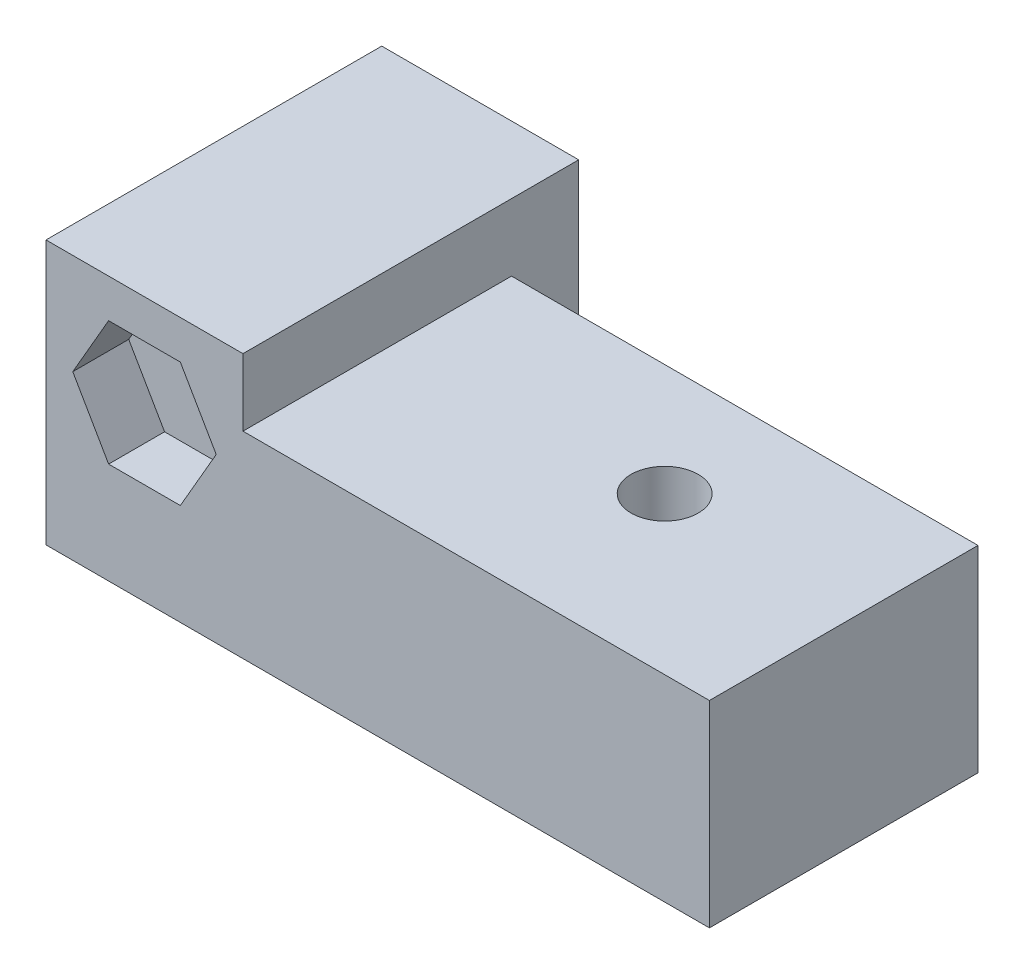
SolidWorks part; units mm, degrees
material "ABS"
ref_plane "前视基准面" through (0, 0, 0) normal (0, 0, 1) x (1, 0, 0)
ref_plane "上视基准面" through (0, 0, 0) normal (0, 1, 0) x (1, 0, 0)
ref_plane "右视基准面" through (0, 0, 0) normal (1, 0, 0) x (0, 0, -1)
sketch "草图1" plane through (0, 0, 0) normal (0, 0, 1) x (1, 0, 0)
  line L0 (-6.8, -0.2195) -> (0, -0.2195)
  line L1 (0, -0.2195) -> (0, -11.2195)
  line L2 (0, -11.2195) -> (-6.8, -11.2195)
  line L4 (-6.8, -8.2195) -> (-2, -8.2195)
  line L5 (-2, -8.2195) -> (-2, -1.2195)
  line L6 (-2, -1.2195) -> (-6.8, -1.2195)
  line L9 (-6.8, -0.2195) -> (-8.8, -0.2195)
  line L10 (-6.8, -1.2195) -> (-6.8, -8.2195)
  line L11 (-6.8, -11.2195) -> (-8.8, -11.2195)
  line L12 (-8.8, -0.2195) -> (-8.8, -11.2195)
  dimension "D1" = 4.8
  dimension "D2" = 7
  dimension "D4" = 2
  dimension "D5" = 1
  dimension "D6" = 3
  dimension "D7" = 2
extrude "凸台-拉伸1" add sketch "草图1" along normal blind 15
sketch "草图2" plane through (-2, 0, 0) normal (-1, 0, 0) x (0, 0, 1)
  line L0 (15, -1.2195) -> (0, -1.2195) construction
  line L1 (15, -8.2195) -> (10, -8.2195)
  line L2 (15, -8.2195) -> (15, -1.2195)
  line L3 (15, -1.2195) -> (10, -1.2195)
  line L4 (10, -8.2195) -> (10, -1.2195)
  dimension "D1" = 5
extrude "凸台-拉伸2" add sketch "草图2" along normal blind 5
sketch "草图3" plane through (0, 0, 15) normal (0, 0, 1) x (1, 0, 0)
  line L1 (-8.8, -11.2195) -> (0, -11.2195) construction
  line L2 (-8.8, -0.2195) -> (-8.8, -11.2195) construction
  circle A0 centre (-4.4, -4.7195) radius 1.5
  dimension "D1" = 3
  dimension "D2" = 4.4
  dimension "D3" = 6.5
extrude "切除-拉伸1" cut sketch "草图3" against normal blind 15
sketch "草图5" plane through (-8.8, 0, 0) normal (-1, 0, 0) x (0, 0, 1)
  line L1 (3, -3.2195) -> (15, -3.2195)
  line L2 (3, -3.2195) -> (3, -12.0195)
  line L3 (3, -12.0195) -> (15, -12.0195)
  line L4 (15, -3.2195) -> (15, -12.0195)
  line L5 (15, -0.2195) -> (0, -0.2195) construction
  dimension "D1" = 3
  dimension "D2" = 8.8
  dimension "D3" = 12
extrude "凸台-拉伸4" add sketch "草图5" against normal blind 29.64
sketch "草图7" plane through (0, 0, 15) normal (0, 0, 1) x (1, 0, 0)
  line L1 (-1.1957, -4.7195) -> (-2.7979, -1.9445)
  line L2 (-2.7979, -1.9445) -> (-6.0021, -1.9445)
  line L3 (-6.0021, -1.9445) -> (-7.6043, -4.7195)
  line L4 (-7.6043, -4.7195) -> (-6.0021, -7.4945)
  line L5 (-6.0021, -7.4945) -> (-2.7979, -7.4945)
  line L6 (-2.7979, -7.4945) -> (-1.1957, -4.7195)
  circle A0 centre (-4.4, -4.7195) radius 2.775 construction
  point P1 (0, 0)
  dimension "D1" = 5.55
extrude "切除-拉伸2" cut sketch "草图7" against normal blind 2.5
sketch "草图8" plane through (0, -11.2195, 0) normal (0, 1, 0) x (-1, 0, 0)
  line L0 (0, 15) -> (0, 0) construction
  line L1 (0, 0) -> (8.8, 0) construction
  circle A0 centre (4.4, 5) radius 1.5
  dimension "D2" = 3
  dimension "D3" = 5
  dimension "D1" = 4.4
extrude "切除-拉伸3" cut sketch "草图8" along normal up to next
sketch "草图9" plane through (0, -11.2195, 0) normal (0, 1, 0) x (-1, 0, 0)
  line L0 (8.8, 15) -> (8.8, 0) construction
  line L1 (8.8, 0.6) -> (0, 0.6)
  line L2 (8.8, 0.6) -> (8.8, 9.4)
  line L3 (8.8, 9.4) -> (0, 9.4)
  line L4 (0, 0.6) -> (0, 9.4)
  line L5 (0, 15) -> (0, 0) construction
  circle A0 centre (4.4, 5) radius 1.5 construction
  dimension "D2" = 4.4
  dimension "D1" = 8.8
extrude "凸台-拉伸5" add sketch "草图9" against normal blind 2
sketch "草图10" plane through (0, -13.2195, 0) normal (0, -1, 0) x (1, 0, 0)
  line L1 (-4.4, 1.7957) -> (-1.625, 3.3979)
  line L2 (-1.625, 3.3979) -> (-1.625, 6.6021)
  line L3 (-1.625, 6.6021) -> (-4.4, 8.2043)
  line L4 (-4.4, 8.2043) -> (-7.175, 6.6021)
  line L5 (-7.175, 6.6021) -> (-7.175, 3.3979)
  line L6 (-7.175, 3.3979) -> (-4.4, 1.7957)
  circle A0 centre (-4.4, 5) radius 2.775 construction
  dimension "D1" = 5.55
extrude "切除-拉伸5" cut sketch "草图10" against normal blind 2.5
sketch "草图11" plane through (0, -3.2195, 0) normal (0, 1, 0) x (-1, 0, 0)
  line L2 (-20.84, 3) -> (0, 3) construction
  line L3 (-20.84, 15) -> (-20.84, 3) construction
  circle A0 centre (-11.84, 8) radius 1.5
  dimension "D1" = 5
  dimension "D2" = 9
  dimension "D3" = 3
extrude "切除-拉伸7" cut sketch "草图11" against normal blind 3.7
sketch "草图12" plane through (0, 0, 0) normal (0, 0, -1) x (-1, 0, 0)
  line L0 (2, -1.2195) -> (6.8, -1.2195)
  line L1 (6.8, -1.2195) -> (6.8, -8.2195)
  line L2 (6.8, -8.2195) -> (2, -8.2195)
  line L3 (2, -8.2195) -> (2, -1.2195)
extrude "切除-拉伸8" cut sketch "草图12" against normal blind 10
